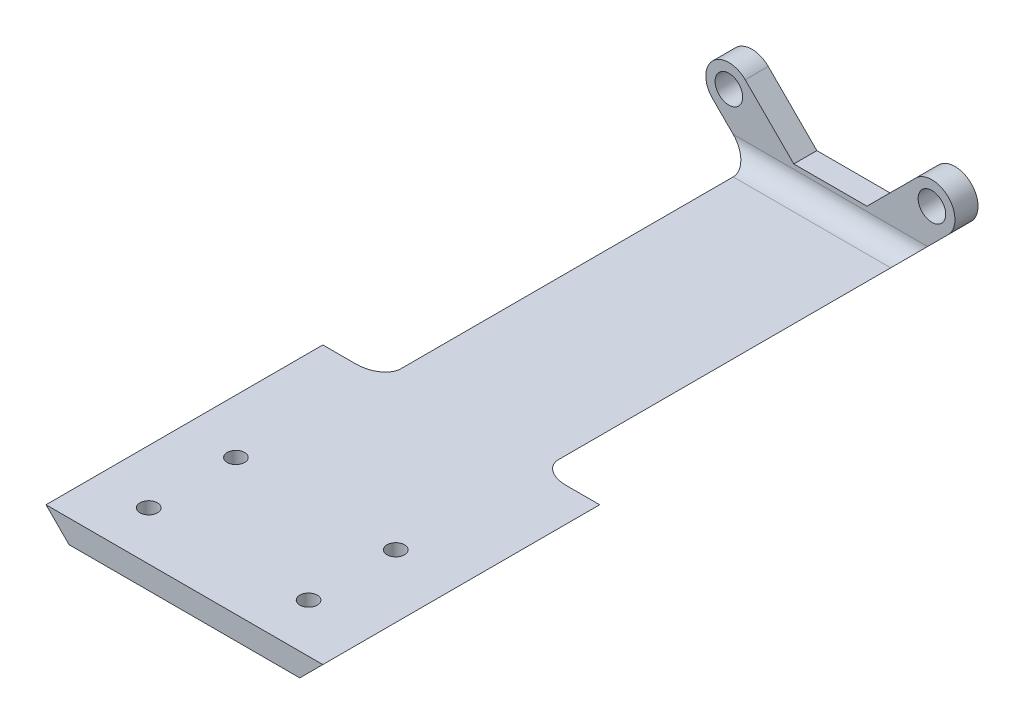
SolidWorks part; units mm, degrees
ref_plane "Front Plane" through (0, 0, 0) normal (0, 0, 1) x (1, 0, 0)
ref_plane "Top Plane" through (0, 0, 0) normal (0, 1, 0) x (1, 0, 0)
ref_plane "Right Plane" through (0, 0, 0) normal (1, 0, 0) x (0, 0, -1)
sketch "Sketch1" plane through (0, 0, 0) normal (0, 0, 1) x (1, 0, 0)
  line L0 (0, 0) -> (7.62, -7.62) construction
  line L1 (7.62, -7.62) -> (20.32, -7.62) construction
  line L2 (20.32, -7.62) -> (27.94, 0) construction
  line L3 (-2.2451, -2.2451) -> (6.3049, -10.795)
  line L4 (6.3049, -10.795) -> (21.6351, -10.795)
  line L5 (21.6351, -10.795) -> (30.1851, -2.2451)
  line L6 (2.2451, 2.2451) -> (8.9351, -4.445)
  line L7 (8.9351, -4.445) -> (19.0049, -4.445)
  line L8 (19.0049, -4.445) -> (25.6949, 2.2451)
  arc A0 (-2.2451, -2.2451) -> (2.2451, 2.2451) centre (0, 0) cw
  arc A1 (30.1851, -2.2451) -> (25.6949, 2.2451) centre (27.94, 0) ccw
  dimension "D1" = 7.62
  dimension "D2" = 7.62
  dimension "D3" = 12.7
  dimension "D4" = 7.62
  dimension "D5" = 3.175
  dimension "D6" = 3.175
extrude "Boss-Extrude1" add sketch "Sketch1" along normal blind 3.175
sketch "Sketch2" plane through (0, 0, 3.175) normal (0, 0, 1) x (1, 0, 0)
  line L0 (13.97, -4.445) -> (13.97, -10.795) construction
  line L1 (19.0049, -4.445) -> (8.9351, -4.445) construction
  line L2 (6.3049, -10.795) -> (21.6351, -10.795) construction
  line L3 (6.3049, -10.795) -> (21.6351, -10.795)
  line L4 (6.3049, -10.795) -> (6.3049, -7.62)
  line L5 (21.6351, -10.795) -> (21.6351, -7.62)
  line L6 (6.3049, -7.62) -> (21.6351, -7.62)
  line L7 (6.3049, -7.62) -> (3.1299, -7.62)
  line L8 (-2.2451, -2.2451) -> (6.3049, -10.795) construction
  line L9 (3.1299, -7.62) -> (6.3049, -10.795)
  line L10 (21.6351, -10.795) -> (24.8101, -7.62)
  line L11 (21.6351, -10.795) -> (30.1851, -2.2451) construction
  line L12 (24.8101, -7.62) -> (21.6351, -7.62)
  line M2 (-2.2451, -2.2451) -> (6.3049, -10.795)
  line M3 (6.3049, -10.795) -> (21.6351, -10.795)
  line M4 (21.6351, -10.795) -> (30.1851, -2.2451)
  dimension "D1" = 3.175
extrude "Boss-Extrude2" add sketch "Sketch2" along normal blind 50.8 contours L0 L6 L4 M3 | L6 L0 L3 L5 | L4 L7 M2 | L12 L5 M4
fillet "Fillet1" radius 2.54 1 edges
hole_wizard "#6 Clearance Hole1" positions "Sketch4" profile "Sketch3" hole size "#6" standard "Ansi Inch"
sketch "Sketch4" plane through (0, 0, 0) normal (0, 0, -1) x (-1, 0, 0)
  arc A0 (-25.6949, 2.2451) -> (-30.1851, -2.2451) centre (-27.94, 0) ccw construction
  arc A3 (2.2451, -2.2451) -> (-2.2451, 2.2451) centre (0, 0) ccw construction
  point P0 (-27.94, 0)
  point P1 (0, 0)
sketch "Sketch3" plane through (27.94, 0, 0) normal (1, 0, 0) x (0, 1, 0)
  line L0 (0, 0) -> (0, 26.5408)
  line L1 (0, 26.5408) -> (1.8986, 25.4)
  line L2 (1.8986, 25.4) -> (1.8986, 0)
  line L5 (1.8986, 0) -> (0, 0)
  line L10 (0, 26.5408) -> (-1.8986, 25.4) construction
  line L11 (0, -6.35) -> (0, 107.95) construction
  dimension "Hole Dia." = 3.7973
  dimension "Hole Depth" = 25.4
  dimension "Drill Angle" = 118
sketch "Sketch7" plane through (0, 0, 53.975) normal (0, 0, 1) x (1, 0, 0)
  line L0 (-5.08, -7.62) -> (33.02, -7.62)
  line L1 (33.02, -7.62) -> (29.845, -10.795)
  line L2 (29.845, -10.795) -> (-1.905, -10.795)
  line L3 (-1.905, -10.795) -> (-5.08, -7.62)
  line L4 (24.8101, -7.62) -> (3.1299, -7.62) construction
  line L5 (6.3049, -10.795) -> (21.6351, -10.795) construction
  line L6 (21.6351, -10.795) -> (24.8101, -7.62) construction
  line L7 (3.1299, -7.62) -> (6.3049, -10.795) construction
  dimension "D1" = 38.1
  dimension "D2" = 8.2099
extrude "Boss-Extrude3" add sketch "Sketch7" along normal blind 38.1
fillet "Fillet2" radius 2.54 2 edges
hole_wizard "M2 Clearance Hole1" positions "Sketch9" profile "Sketch8" hole size "M2" standard "Ansi Metric"
sketch "Sketch9" plane through (0, -7.62, 0) normal (0, 1, 0) x (-1, 0, 0)
  line L0 (-33.02, 79.375) -> (5.08, 79.375) construction
  line L1 (-33.02, 92.075) -> (-33.02, 53.975) construction
  line L2 (5.08, 92.075) -> (5.08, 53.975) construction
  line L5 (-2.3543, 85.375) -> (-24.3543, 85.375)
  line L6 (-2.3543, 85.375) -> (-2.3543, 73.375)
  line L7 (-2.3543, 73.375) -> (-24.3543, 73.375)
  line L8 (-24.3543, 85.375) -> (-24.3543, 73.375)
  line L9 (-2.3543, 85.375) -> (-24.3543, 73.375) construction
  line L10 (-2.3543, 73.375) -> (-24.3543, 85.375) construction
  point P0 (-2.3543, 85.375)
  point P1 (-2.3543, 73.375)
  point P3 (-24.3543, 85.375)
  point P5 (-24.3543, 73.375)
  dimension "D1" = 22
  dimension "D2" = 12
  dimension "D3" = 25.4
sketch "Sketch8" plane through (2.3543, -7.62, 85.375) normal (1, 0, 0) x (0, 0, 1)
  line L0 (0, 0) -> (0, 26.121)
  line L1 (0, 26.121) -> (1.2, 25.4)
  line L2 (1.2, 25.4) -> (1.2, 0)
  line L5 (1.2, 0) -> (0, 0)
  line L10 (0, 26.121) -> (-1.2, 25.4) construction
  line L11 (0, -6.35) -> (0, 107.95) construction
  dimension "Hole Dia." = 2.4
  dimension "Hole Depth" = 25.4
  dimension "Drill Angle" = 118
